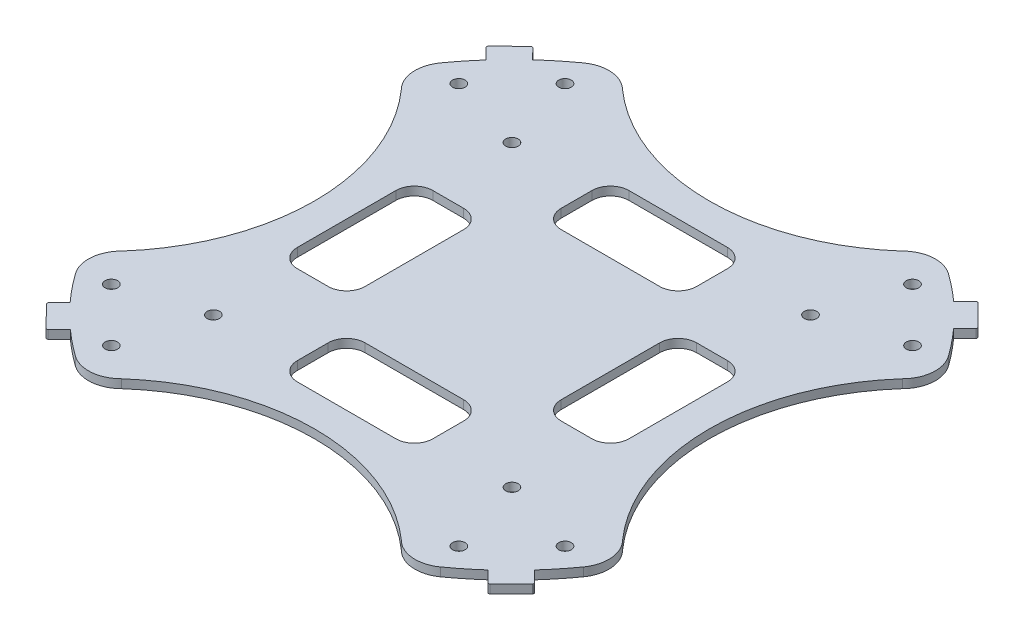
SolidWorks part; units mm, degrees
ref_plane "Front Plane" through (0, 0, 0) normal (0, 0, 1) x (1, 0, 0)
ref_plane "Top Plane" through (0, 0, 0) normal (0, 1, 0) x (1, 0, 0)
ref_plane "Right Plane" through (0, 0, 0) normal (1, 0, 0) x (0, 0, -1)
sketch "Sketch1" plane through (0, 0, 0) normal (0, 1, 0) x (1, 0, 0)
  line L0 (-1000, 0) -> (49000, 0) construction
  line L1 (0, -1000) -> (0, 49000) construction
  line L2 (707.1069, -707.1069) -> (-34648.2322, 34648.2322) construction
  line L3 (-707.1068, -707.1068) -> (34648.2323, 34648.2323) construction
  line L4 (716.0871, -698.1266) -> (0, 17.9605) construction
  line L5 (-698.1265, -716.087) -> (34657.2125, 34639.252) construction
  line L6 (698.1266, -716.0871) -> (-34657.2125, 34639.2519) construction
  line L7 (-716.087, -698.1265) -> (0, 17.9605) construction
  line L8 (-733.6258, -670.2104) -> (-31.7077, 31.7077) construction
  line L9 (733.9751, -670.5597) -> (22.7274, 40.6879) construction
  line L10 (39.5829, 36.115) -> (36.1358, 39.5583)
  line L11 (716.0871, -698.1266) -> (-34639.2519, 34657.2125) construction
  line L12 (35.7817, 39.5534) -> (33.9856, 37.7573)
  line L13 (-716.087, -698.1265) -> (34639.252, 34657.2125) construction
  line L14 (39.5739, 35.7609) -> (37.7573, 33.9856)
  line L15 (39.5382, -36.1548) -> (36.0819, -39.6111)
  line L16 (39.5078, -35.8322) -> (37.7118, -34.0362)
  line L17 (-35.9968, -39.6764) -> (-39.3444, -36.2512)
  line L18 (-37.6038, -34.1555) -> (-39.3423, -35.894)
  line L19 (35.7129, -39.6171) -> (33.9376, -37.8006)
  line L20 (-35.6141, -39.7036) -> (-33.8181, -37.9075)
  line L21 (-39.7221, 35.8999) -> (-36.251, 39.2922)
  line L22 (-34.2033, 37.5603) -> (-35.8918, 39.2881)
  line L24 (-37.9528, 33.7672) -> (-39.7242, 35.5386)
  line L30 (-39.4203, -35.9308) -> (-37.6038, -34.1555) [skipped]
  line L31 (-39.7488, 35.5633) -> (-37.9528, 33.7672) [skipped]
  line L32 (-35.9786, 39.3768) -> (-34.2033, 37.5603) [skipped]
  arc A0 (-29.6486, 41.2505) -> (-34.2033, 37.5603) centre (0, 0) ccw construction
  arc A1 (-22.7274, 40.6879) -> (-29.6486, 41.2505) centre (-26.519, 36.8963) ccw
  arc A2 (-40.6879, 22.7274) -> (-41.2505, 29.6486) centre (-36.8963, 26.519) cw
  arc A3 (22.7274, 40.6879) -> (29.6486, 41.2505) centre (26.519, 36.8963) cw
  arc A4 (40.6879, 22.7274) -> (41.2505, 29.6486) centre (36.8963, 26.519) ccw
  arc A5 (40.6879, -22.7274) -> (41.2505, -29.6486) centre (36.8963, -26.519) cw
  arc A6 (22.7274, -40.6879) -> (29.6486, -41.2505) centre (26.519, -36.8963) ccw
  arc A7 (-22.7274, -40.6879) -> (-29.6486, -41.2505) centre (-26.519, -36.8963) cw
  arc A8 (-40.6879, -22.7274) -> (-41.2505, -29.6486) centre (-36.8963, -26.519) ccw
  arc A9 (-22.7274, 40.6879) -> (22.7274, 40.6879) centre (0, 66.2866) ccw
  arc A10 (40.6879, 22.7274) -> (40.6879, -22.7274) centre (66.2866, 0) ccw
  arc A11 (22.7274, -40.6879) -> (-22.7274, -40.6879) centre (0, -66.2866) ccw
  arc A12 (-40.6879, -22.7274) -> (-40.6879, 22.7274) centre (-66.2866, 0) ccw
  arc A13 (-29.6486, 41.2505) -> (-34.2033, 37.5603) centre (0, 0) ccw
  arc A14 (41.2505, 29.6486) -> (37.7573, 33.9856) centre (0, 0) ccw construction
  arc A15 (41.2505, 29.6486) -> (37.7573, 33.9856) centre (0, 0) ccw
  arc A16 (29.6486, -41.2505) -> (33.9376, -37.8006) centre (0, 0) ccw construction
  arc A17 (29.6486, -41.2505) -> (33.9376, -37.8006) centre (0, 0) ccw
  arc A18 (-41.2505, -29.6486) -> (-37.6038, -34.1555) centre (0, 0) ccw construction
  arc A19 (-41.2505, -29.6486) -> (-37.6038, -34.1555) centre (0, 0) ccw
  arc A20 (33.9856, 37.7573) -> (29.6486, 41.2505) centre (0, 0) ccw construction
  arc A21 (33.9856, 37.7573) -> (29.6486, 41.2505) centre (0, 0) ccw
  arc A22 (37.7118, -34.0362) -> (41.2505, -29.6486) centre (0, 0) ccw construction
  arc A23 (37.7118, -34.0362) -> (41.2505, -29.6486) centre (0, 0) ccw
  arc A24 (-33.8181, -37.9075) -> (-29.6486, -41.2505) centre (0, 0) ccw construction
  arc A25 (-33.8181, -37.9075) -> (-29.6486, -41.2505) centre (0, 0) ccw
  arc A26 (-37.9528, 33.7672) -> (-41.2505, 29.6486) centre (0, 0) ccw construction
  arc A27 (-37.9528, 33.7672) -> (-41.2505, 29.6486) centre (0, 0) ccw
  arc A28 (-35.6141, -39.7036) -> (-35.9968, -39.6764) centre (-35.7937, -39.5239) cw
  arc A29 (-39.3423, -35.894) -> (-39.3444, -36.2512) centre (-39.1627, -36.0736) ccw
  arc A30 (35.7129, -39.6171) -> (36.0819, -39.6111) centre (35.8945, -39.4396) ccw
  arc A31 (39.5078, -35.8322) -> (39.5382, -36.1548) centre (39.3282, -36.0118) cw
  arc A32 (39.5739, 35.7609) -> (39.5829, 36.115) centre (39.3964, 35.9426) ccw
  arc A33 (36.1358, 39.5583) -> (35.7817, 39.5534) centre (35.9613, 39.3738) ccw
  arc A34 (-39.7221, 35.8999) -> (-39.7242, 35.5386) centre (-39.5446, 35.7182) ccw
  arc A35 (-36.251, 39.2922) -> (-35.8918, 39.2881) centre (-36.0735, 39.1105) cw
  circle A36 centre (-28.2202, 36.8412) radius 1.016
  circle A37 centre (-36.8412, 28.2202) radius 1.016
  circle A38 centre (-24.2455, 24.2455) radius 1.016
  circle A39 centre (28.2202, 36.8412) radius 1.016
  circle A40 centre (36.8412, 28.2202) radius 1.016
  circle A41 centre (24.2455, 24.2455) radius 1.016
  circle A42 centre (36.8412, -28.2202) radius 1.016
  circle A43 centre (28.2202, -36.8412) radius 1.016
  circle A44 centre (24.2455, -24.2455) radius 1.016
  circle A45 centre (-28.2202, -36.8412) radius 1.016
  circle A46 centre (-36.8412, -28.2202) radius 1.016
  circle A47 centre (-24.2455, -24.2455) radius 1.016
  point P46 (0, 0)
  point P60 (0, 0)
  point P75 (-0.048, -0.2069)
  point P83 (41.6473, 37.8756)
  point P86 (37.8756, 41.6473)
  point P120 (0, 0)
  dimension "D1" = 12.7
  dimension "D3" = 4
  dimension "D4" = 4
  dimension "D7" = 0.254
  dimension "D8" = 50.8
  dimension "D10" = 0.254
  dimension "D9" = 0.254
  dimension "D13" = 13.208
  dimension "D5" = 2.667
  dimension "D11" = 12.192
  dimension "D12" = 7.366
  dimension "D2" = 12.7
  dimension "D6" = 4
  dimension "D14" = 4
extrude "Boss-Extrude1" add sketch "Sketch1" along normal blind 1.397
sketch "Sketch3" plane through (0, 1.397, 0) normal (0, 1, 0) x (1, 0, 0)
  line L0 (0, 0) -> (0, 50000) construction
  line L1 (26.924, 8.076) -> (26.924, -7.924)
  line L2 (-8, 27) -> (8, 27)
  line L3 (-11, 24) -> (-11, 19)
  line L4 (-8, 16) -> (8, 16)
  line L5 (11, 24) -> (11, 19)
  line L6 (-11, 27) -> (11, 16) construction
  line L7 (-11, 16) -> (11, 27) construction
  line L8 (23.924, -10.924) -> (18.924, -10.924)
  line L9 (15.924, 8.076) -> (15.924, -7.924)
  line L10 (23.924, 11.076) -> (18.924, 11.076)
  line L11 (8, -26.848) -> (-8, -26.848)
  line L12 (-11, -23.848) -> (-11, -18.848)
  line L13 (8, -15.848) -> (-8, -15.848)
  line L14 (11, -23.848) -> (11, -18.848)
  line L15 (-26.924, -7.924) -> (-26.924, 8.076)
  line L16 (-23.924, 11.076) -> (-18.924, 11.076)
  line L17 (-15.924, -7.924) -> (-15.924, 8.076)
  line L18 (-23.924, -10.924) -> (-18.924, -10.924)
  arc A0 (-11, 24) -> (-8, 27) centre (-8, 24) cw
  arc A1 (-11, 19) -> (-8, 16) centre (-8, 19) ccw
  arc A2 (11, 19) -> (8, 16) centre (8, 19) cw
  arc A3 (11, 24) -> (8, 27) centre (8, 24) ccw
  arc A4 (23.924, 11.076) -> (26.924, 8.076) centre (23.924, 8.076) cw
  arc A5 (23.924, -10.924) -> (26.924, -7.924) centre (23.924, -7.924) ccw
  arc A6 (18.924, 11.076) -> (15.924, 8.076) centre (18.924, 8.076) ccw
  arc A7 (18.924, -10.924) -> (15.924, -7.924) centre (18.924, -7.924) cw
  arc A8 (11, -23.848) -> (8, -26.848) centre (8, -23.848) cw
  arc A9 (-11, -23.848) -> (-8, -26.848) centre (-8, -23.848) ccw
  arc A10 (11, -18.848) -> (8, -15.848) centre (8, -18.848) ccw
  arc A11 (-11, -18.848) -> (-8, -15.848) centre (-8, -18.848) cw
  arc A12 (-23.924, -10.924) -> (-26.924, -7.924) centre (-23.924, -7.924) cw
  arc A13 (-23.924, 11.076) -> (-26.924, 8.076) centre (-23.924, 8.076) ccw
  arc A14 (-18.924, -10.924) -> (-15.924, -7.924) centre (-18.924, -7.924) ccw
  arc A15 (-18.924, 11.076) -> (-15.924, 8.076) centre (-18.924, 8.076) cw
  point P3 (0, 21.5)
  point P59 (0, 0.076)
  dimension "D3" = 27
  dimension "D4" = 3
  dimension "D1" = 11
  dimension "D2" = 22
  dimension "D5" = 4
extrude "Cut-Extrude1" cut sketch "Sketch3" against normal blind 1.397
